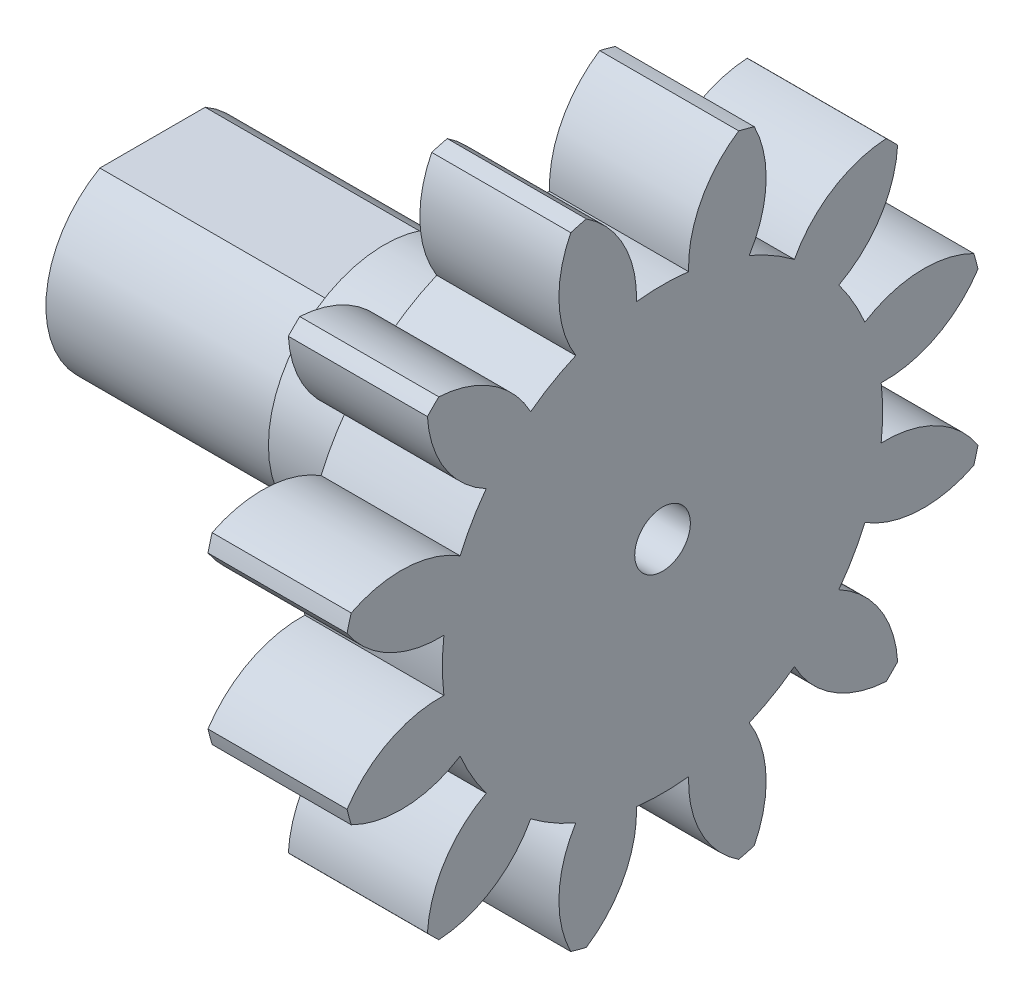
SolidWorks part; units mm, degrees
ref_plane "Plane1" through (0, 0, 0) normal (0, 0, 1) x (1, 0, 0)
ref_plane "Plane2" through (0, 0, 0) normal (0, 1, 0) x (1, 0, 0)
ref_plane "Plane3" through (0, 0, 0) normal (1, 0, 0) x (0, 0, -1)
sketch "HoldingSke" plane through (0, 0, 0) normal (0, 1, 0) x (1, 0, 0)
  line L0 (0, 0) -> (0.9781, -0.2079)
  line L1 (-15, 0) -> (100, 0) construction
  line L2 (0, 0) -> (-2.1039, 2.3779)
  line L3 (0, 0) -> (-11.863, 4.5341)
  line L4 (0, 0) -> (8.4473, 1.7955)
  line L5 (0, 0) -> (-14.0543, -5.2418)
  line L6 (0, 0) -> (-2.4869, -1.6779)
  line L7 (-2.1039, 2.3779) -> (1.1249, 17.0263)
  line L8 (-76.2, 54.61) -> (-75.7, 54.61)
  line L9 (-71.009, 38.7566) -> (-53.1078, 45.2721)
  line L10 (-76.2, 71.12) -> (104.1128, 71.12)
  line L11 (0, 0) -> (-3, 0)
  line L12 (-76.2, 101.6) -> (-76.162, 101.6)
  line L13 (24.9733, 27.94) -> (52.9518, 28.4284)
  line L14 (24.9733, 27.94) -> (24.9743, 27.94)
  line L15 (24.9733, 27.94) -> (100.4006, 29.5858)
  line L16 (-63.627, -1) -> (-12.827, -1)
  circle A0 centre (0, 0) radius 1.5
  circle A1 centre (0, 0) radius 2.5
  circle A2 centre (0, 0) radius 2.5
  circle A3 centre (0, 0) radius 1.5
  dimension "MHD" = 5
  dimension "Hub_dia" = 5
  dimension "Bore" = 3
  dimension "MBD" = 3
  dimension "Num_teeth" = 12
  dimension "Pitch" = 1
  dimension "Overall_len" = 15
  dimension "Show_teeth" = 12
  dimension "Thickness" = 3
  dimension "OAL" = 15.0001
  dimension "T_dim" = 0.5
  dimension "Ap" = 20
  dimension "H" = 19.05
  dimension "Pitch_radius" = 180.3128
  dimension "Width" = 3
  dimension "Backlash" = 0.038
  dimension "Addendum_fac" = 1
  dimension "Dedendum_fac" = 1.25
  dimension "Clearance_fac" = 0.25
  dimension "Dedendum_add" = 0.001
  dimension "Module" = 1
sketch "BasProSke" plane through (0, 0, 0) normal (0, 1, 0) x (1, 0, 0)
  line L0 (-10, 0) -> (60, 0) construction
  line L1 (0, 0) -> (0, 7)
  line L2 (0, 0) -> (3, 0)
  line L3 (3, 0) -> (3, 7)
  line L4 (3, 7) -> (0, 7)
  dimension "Thickness" = 3
  dimension "Diameter" = 14
revolve "Base-Revolve" add sketch "BasProSke" angle 360 about L0
sketch "TooCutSke" plane through (0, 0, 0) normal (1, 0, 0) x (0, 0, -1)
  line L1 (0, 0) -> (0, 107) construction
  line L2 (0, 0) -> (-0.8496, 5.9395) construction
  line L3 (0, 0) -> (-3.0836, 11.5081) construction
  line L4 (-0.8496, 5.9395) -> (-1.5418, 5.7541) construction
  arc A0 (0.5622, 4.7156) -> (-0.5622, 4.7156) centre (0, 0) ccw
  arc A1 (1.6729, 6.8233) -> (-1.6729, 6.8233) centre (0, 0) ccw
  circle A2 centre (0, 0) radius 6 construction
  circle A3 centre (0, 0) radius 5.6382 construction
  arc A4 (-0.5622, 4.7156) -> (-1.6729, 6.8233) centre (-2.9608, 4.7982) ccw
  arc A5 (1.6729, 6.8233) -> (0.5622, 4.7156) centre (2.9608, 4.7982) ccw
  dimension "Root_dia" = 9.498
  dimension "Overcut_dia" = 14.0508
  dimension "Pitch_dia" = 12
  dimension "Base_dia" = 11.2763
  dimension "Flank_rad" = 2.4
  dimension "Half_ang" = 15
  dimension "Half_CT" = 0.7167
extrude "ToothCut" cut sketch "TooCutSke" along normal through all
fillet "Breaks" [suppressed] radius 0.02
fillet "RootFillets" [suppressed] radius 0.251
pattern_circular "TeethCuts" count 12 over 360 about axis through (0, 0, 0) along (1, 0, 0) of "ToothCut", "RootFillets", "Breaks"
sketch "HubNeaOneSke" plane through (0, 0, 0) normal (-1, 0, 0) x (0, 0, 1)
  circle A0 centre (0, 0) radius 2.5
  dimension "Diameter" = 5
extrude "HubNearOne" add sketch "HubNeaOneSke" along normal blind 8
sketch "HubNeaBotSke" plane through (0, 0, 0) normal (-1, 0, 0) x (0, 0, 1)
  circle A0 centre (0, 0) radius 2.5
  dimension "Diameter" = 5
extrude "HubNearBoth" [suppressed] add sketch "HubNeaBotSke" along normal blind 6
ref_plane "FarPln" through (3, 0, 0) normal (1, 0, 0) x (0, 0, -1)
sketch "HubFarSke" plane through (3, 0, 0) normal (1, 0, 0) x (0, 0, -1)
  circle A0 centre (0, 0) radius 2.5
  dimension "Diameter" = 5
extrude "HubFar" [suppressed] add sketch "HubFarSke" along normal blind 6
sketch "BorSke" plane through (0, 0, 0) normal (1, 0, 0) x (0, 0, -1)
  circle A0 centre (0, 0) radius 0.6
  dimension "Diameter" = 1.2
extrude "Bore" cut sketch "BorSke" along normal mid plane 30.0001
sketch "KeySke" plane through (0, 0, 0) normal (1, 0, 0) x (0, 0, -1)
  line L0 (-0.6, 0) -> (-0.6, 2)
  line L1 (-0.6, 2) -> (0.6, 2)
  line L2 (0.6, 2) -> (0.6, 0)
  line L3 (0, 0) -> (0, 34) construction
  line L4 (-0.6, 0) -> (0.6, 0)
  dimension "Offset" = 2
  dimension "Width" = 1.2
extrude "Keyway" [suppressed] cut sketch "KeySke" along normal mid plane 30.0001
pattern_circular "Keyway2" [suppressed] count 2 every 90 about axis through (-10, 0, 0) along (1, 0, 0)
sketch "草图1" plane through (-8, 0, 0) normal (-1, 0, 0) x (0, 0, 1)
  line L0 (-1.5, 2) -> (1.5, 2)
  arc A0 (1.5, 2) -> (-1.5, 2) centre (0, 0) ccw
  circle A1 centre (0, 0) radius 2.5 construction
  dimension "D1" = 2
extrude "切除-拉伸4" cut sketch "草图1" against normal blind 5
sketch "草图2" plane through (0, 0, 0) normal (-1, 0, 0) x (0, 0, 1)
  circle A0 centre (0, 0) radius 3
  circle A1 centre (0, 0) radius 2.5
  dimension "D1" = 6
  dimension "D2" = 5
extrude "凸台-拉伸1" add sketch "草图2" along normal blind 0.5
sketch "草图3" plane through (-8, 0, 0) normal (-1, 0, 0) x (0, 0, 1)
  circle A0 centre (0, 0) radius 2.3
  arc A1 (-1.5, 2) -> (1.5, 2) centre (0, 0) ccw construction
  dimension "D1" = 0.2
extrude "切除-拉伸5" cut sketch "草图3" against normal blind 5 flip side to cut
equation "' \"Module@HoldingSke\" = 6.35"
equation "' \"Num_teeth@HoldingSke\" = 12"
equation "' \"Ap@HoldingSke\" =  20"
equation "' \"Ap@HoldingSke\" = 20"
equation "' \"Width@HoldingSke\" = 0.5 * 25.4"
equation "' \"Hub_dia@HoldingSke\"= 1 * 25.4"
equation "' \"Hub_dia@HoldingSke\" = 1 * 25.4"
equation "' \"Overall_len@HoldingSke\" = 1.0 * 25.4"
equation "' \"Bore@HoldingSke\" = 0.75 * 25.4"
equation "' \"T_dim@HoldingSke\" = 0.1 * 25.4"
equation "' \"Width@KeySke\" = 0.25 * 25.4"
equation "' \"Show_teeth@HoldingSke\" = 13"
equation "' \"Backlash@HoldingSke\" = 0.009 * 25.4"
equation "' \"Addendum_fac@HoldingSke\" = 1.0"
equation "' \"Dedendum_fac@HoldingSke\" = 1.25"
equation "' \"Dedendum_add@HoldingSke\" = 0.00005 * 25.4"
equation "' \"Clearance_fac@HoldingSke\" = 0.25"
equation "\"Pitch@HoldingSke\" = 1 / \"Module@HoldingSke\""
equation "\"Overcut_dia@TooCutSke\" = (\"Num_teeth@HoldingSke\" + 2 * \"Addendum_fac@HoldingSke\") / \"Pitch@HoldingSke\" + 0.002 * 25.4"
equation "\"Pitch_dia@TooCutSke\" = \"Num_teeth@HoldingSke\" / \"Pitch@HoldingSke\""
equation "\"Base_dia@TooCutSke\" = \"Num_teeth@HoldingSke\" / \"Pitch@HoldingSke\" * cos((\"Ap@HoldingSke\"  * 3.14159265 / 180))"
equation "\"Root_dia@TooCutSke\" = (\"Num_teeth@HoldingSke\" + 2) / \"Pitch@HoldingSke\" - 2 * (\"Addendum_fac@HoldingSke\" + \"Dedendum_fac@HoldingSke\") / \"Pitch@HoldingSke\" - \"Dedendum_add@HoldingSke\" * 2"
equation "\"Half_ang@TooCutSke\" = 180 / \"Num_teeth@HoldingSke\""
equation "\"Half_CT@TooCutSke\" = \"Num_teeth@HoldingSke\" / \"Pitch@HoldingSke\" * sin((3.14159265 / 2 / \"Num_teeth@HoldingSke\")) / 2 - 7 * \"Backlash@HoldingSke\" / 4"
equation "\"Flank_rad@TooCutSke\" = \"Num_teeth@HoldingSke\" / \"Pitch@HoldingSke\" / 5"
equation "\"Radius@RootFillets\" = \"Clearance_fac@HoldingSke\" / \"Pitch@HoldingSke\" + \"Dedendum_add@HoldingSke\""
equation "\"Break_rad@Breaks\" = 0.02 / \"Pitch@HoldingSke\""
equation "\"Thickness@HoldingSke\" = \"Width@HoldingSke\""
equation "\"OAL@HoldingSke\" = \"Thickness@HoldingSke\""
equation "\"MHD@HoldingSke\" = (\"Num_teeth@HoldingSke\" + 2) / \"Pitch@HoldingSke\" - 2 * (\"Addendum_fac@HoldingSke\" + \"Dedendum_fac@HoldingSke\")  / \"Pitch@HoldingSke\" - \"Dedendum_add@HoldingSke\" * 2"
equation "\"MBD@HoldingSke\" = (\"Num_teeth@HoldingSke\" + 2) / \"Pitch@HoldingSke\" - 2 * (\"Addendum_fac@HoldingSke\" + \"Dedendum_fac@HoldingSke\")  / \"Pitch@HoldingSke\" - \"Dedendum_add@HoldingSke\" * 2 - 0.002 * 25.4"
equation "\"MHD@HoldingSke\" = ((sgn( \"MHD@HoldingSke\" - \"Hub_dia@HoldingSke\" )-1)*( \"MHD@HoldingSke\" - \"Hub_dia@HoldingSke\" ))/-2+ \"Hub_dia@HoldingSke\""
equation "\"MBD@HoldingSke\" = ((sgn( \"MBD@HoldingSke\" - \"Bore@HoldingSke\" )-1)*( \"MBD@HoldingSke\" - \"Bore@HoldingSke\" ))/-2+ \"Bore@HoldingSke\""
equation "\"OAL@HoldingSke\" = ((sgn( \"OAL@HoldingSke\" - \"Overall_len@HoldingSke\" )+1)*( \"OAL@HoldingSke\" - \"Overall_len@HoldingSke\" ))/2 + \"Overall_len@HoldingSke\" + 0.000002 * 25.4"
equation "\"Num_teeth@TeethCuts\" = int( \"Show_teeth@HoldingSke\" ) + 1"
equation "\"Num_teeth@TeethCuts\" = ((sgn( \"Num_teeth@TeethCuts\" - \"Num_teeth@HoldingSke\" )-1)*( \"Num_teeth@TeethCuts\" - \"Num_teeth@HoldingSke\" ))/-2+ \"Num_teeth@HoldingSke\""
equation "\"Num_teeth@TeethCuts\" = ((sgn( \"Num_teeth@TeethCuts\" - 2.0)+1)*( \"Num_teeth@TeethCuts\" - 2.0))/2 +2.0"
equation "\"Angle@TeethCuts\" = 360.0 / \"Num_teeth@HoldingSke\""
equation "\"Diameter@BasProSke\" = (\"Num_teeth@HoldingSke\" + 2 * \"Addendum_fac@HoldingSke\") / \"Pitch@HoldingSke\""
equation "\"Thickness@BasProSke\"  = \"Thickness@HoldingSke\""
equation "' \"Fillet_rad@BasProSke\" =  \"Thickness@HoldingSke\" * 0.05"
equation "' \"Fillet_rad@BasProSke\" = \"Thickness@HoldingSke\" * 0.05"
equation "\"MHD@HoldingSke\" = ((sgn( \"MHD@HoldingSke\" - \"Root_dia@TooCutSke\" )-1)*( \"MHD@HoldingSke\" - \"Root_dia@TooCutSke\" ))/-2+ \"Root_dia@TooCutSke\""
equation "\"Diameter@HubNeaBotSke\" = \"MHD@HoldingSke\""
equation "\"Length@HubNearBoth\" = ( \"OAL@HoldingSke\" - \"Thickness@BasProSke\" ) / 2.0"
equation "\"Thickness@FarPln\" = \"Thickness@BasProSke\""
equation "\"Diameter@HubFarSke\" = \"MHD@HoldingSke\""
equation "\"Length@HubFar\" = ( \"OAL@HoldingSke\" - \"Thickness@BasProSke\" ) / 2.0"
equation "\"D1@Bore\" = \"OAL@HoldingSke\" * 2.0"
equation "\"D1@Keyway\" = \"OAL@HoldingSke\" * 2.0"
equation "\"Offset@KeySke\" = \"T_dim@HoldingSke\" + \"MBD@HoldingSke\" / 2.0"
